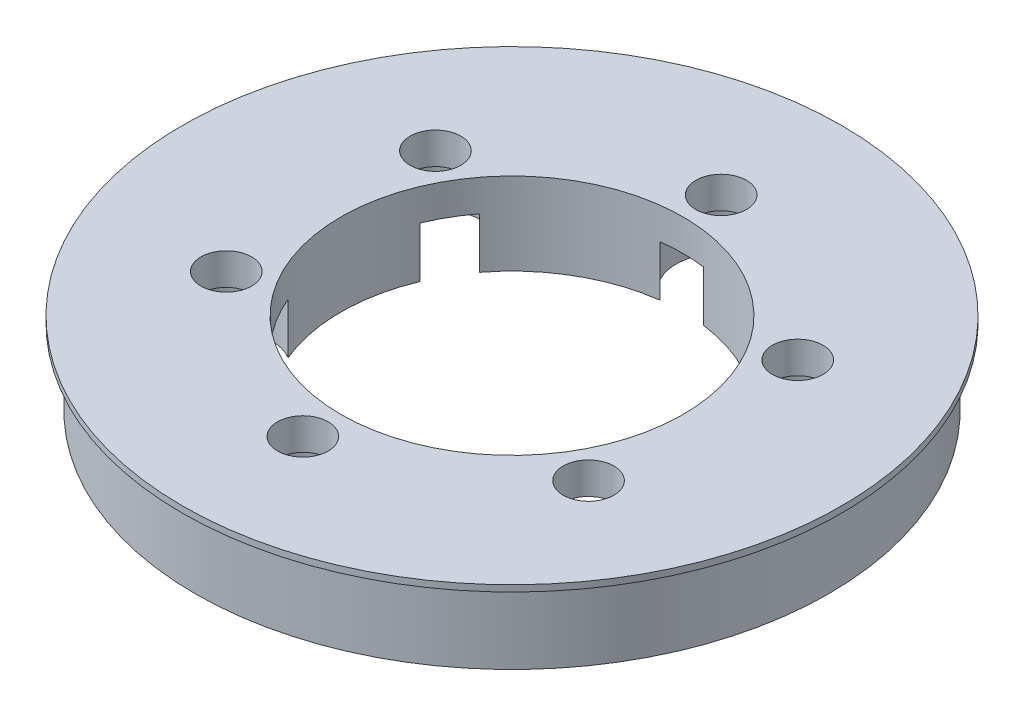
SolidWorks part; units mm, degrees
ref_plane "Front Plane" through (0, 0, 0) normal (0, 0, 1) x (1, 0, 0)
ref_plane "Top Plane" through (0, 0, 0) normal (0, 1, 0) x (1, 0, 0)
ref_plane "Right Plane" through (0, 0, 0) normal (1, 0, 0) x (0, 0, -1)
sketch "Sketch1" plane through (0, 0, 0) normal (0, 1, 0) x (1, 0, 0)
  circle A0 centre (0, 0) radius 25
  circle A1 centre (0, 0) radius 13.5
  dimension "D1" = 50
  dimension "D2" = 27
extrude "Boss-Extrude1" add sketch "Sketch1" along normal blind 6
sketch "Sketch2" plane through (0, 6, 0) normal (0, 1, 0) x (1, 0, 0)
  circle A0 centre (0, 16.5) radius 2
  dimension "D1" = 16.5
  dimension "D2" = 4
extrude "Cut-Extrude1" cut sketch "Sketch2" against normal through all
sketch "Sketch3" plane through (0, 0, 0) normal (0, 1, 0) x (1, 0, 0)
  circle A0 centre (0, 16.5) radius 3.55
  dimension "D1" = 7.1
extrude "Cut-Extrude4" cut sketch "Sketch3" along normal blind 4
pattern_circular "CirPattern2" count 6 over 360 about axis through (0, 0, 0) along (0, 1, 0) of "Cut-Extrude1", "Cut-Extrude4"
sketch "Sketch4" plane through (0, 6, 0) normal (0, 1, 0) x (1, 0, 0)
  circle A0 centre (0, 0) radius 26
  circle A1 centre (0, 0) radius 25 construction
  circle A2 centre (-14.2894, 8.25) radius 2 construction
  circle A3 centre (14.2894, 8.25) radius 2 construction
  circle A4 centre (14.2894, -8.25) radius 2 construction
  circle A5 centre (0, -16.5) radius 2 construction
  circle A6 centre (0, 0) radius 13.5 construction
  circle A7 centre (-14.2894, -8.25) radius 2 construction
  circle A8 centre (0, 16.5) radius 2 construction
  circle A9 centre (14.2894, 8.25) radius 2
  circle A10 centre (14.2894, -8.25) radius 2
  circle A11 centre (0, -16.5) radius 2
  circle A12 centre (0, 0) radius 13.5
  circle A13 centre (-14.2894, -8.25) radius 2
  circle A14 centre (-14.2894, 8.25) radius 2
  circle A15 centre (0, 16.5) radius 2
  dimension "D1" = 1
extrude "Boss-Extrude3" add sketch "Sketch4" along normal blind 0.5
